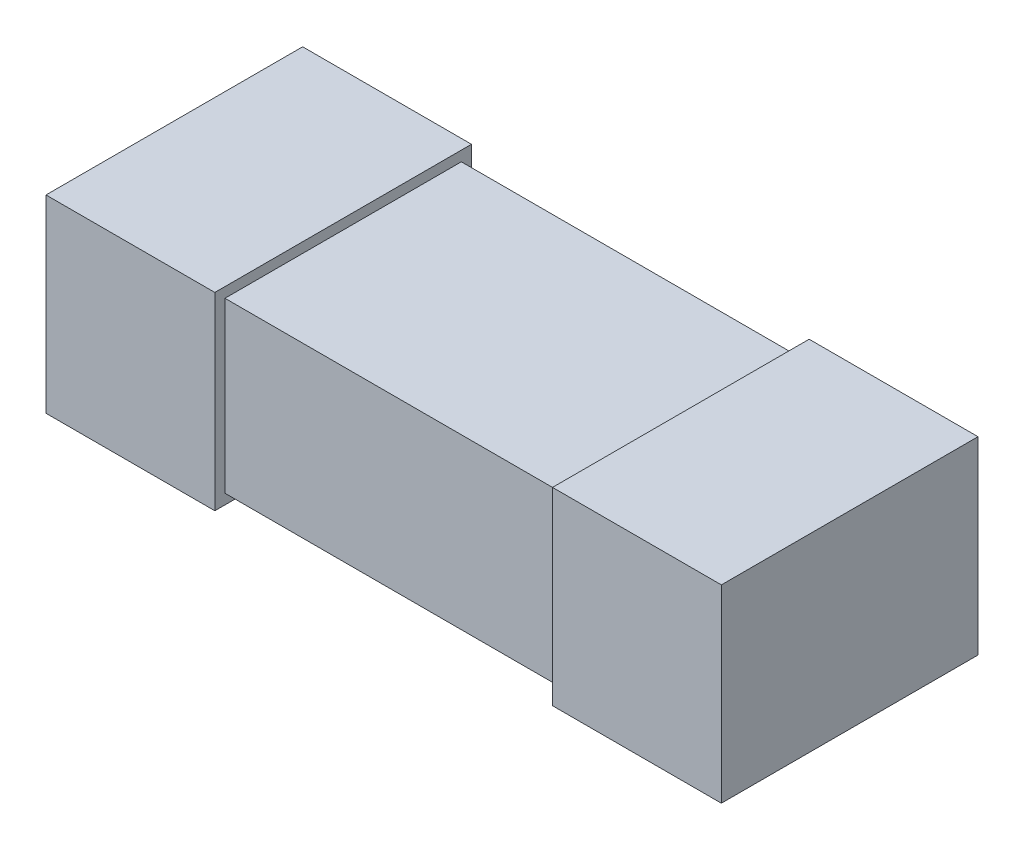
SolidWorks part; units mm, degrees
ref_plane "Front Plane" through (0, 0, 0) normal (0, 0, 1) x (1, 0, 0)
ref_plane "Top Plane" through (0, 0, 0) normal (0, 1, 0) x (1, 0, 0)
ref_plane "Right Plane" through (0, 0, 0) normal (1, 0, 0) x (0, 0, -1)
sketch "Sketch1" plane through (0, 0, 0) normal (0, 1, 0) x (1, 0, 0)
  line L0 (0, 0.35) -> (0, -0.35) construction
  line L1 (-1, -0.35) -> (1, -0.35)
  line L2 (-1, -0.35) -> (-1, 0.35)
  line L3 (-1, 0.35) -> (1, 0.35)
  line L4 (1, -0.35) -> (1, 0.35)
  dimension "D1" = 0.7
  dimension "D2" = 2
extrude "Boss-Extrude1" add sketch "Sketch1" along normal blind 0.5
sketch "Sketch2" plane through (-1, 0, 0) normal (-1, 0, 0) x (0, 0, 1)
  line L0 (-0.35, 0.5) -> (-0.35, 0) construction
  line L1 (-0.38, -0.03) -> (0.38, -0.03)
  line L2 (-0.38, -0.03) -> (-0.38, 0.53)
  line L3 (-0.38, 0.53) -> (0.38, 0.53)
  line L4 (0.38, -0.03) -> (0.38, 0.53)
  line L5 (-0.35, 0) -> (0.35, 0) construction
  line L6 (-0.35, 0.5) -> (0.35, 0.5) construction
  line L7 (0.35, 0.5) -> (0.35, 0) construction
  dimension "D1" = 0.03
  dimension "D2" = 0.03
  dimension "D3" = 0.03
  dimension "D4" = 0.03
extrude "Boss-Extrude2" add sketch "Sketch2" against normal blind 0.5
mirror "Mirror1" about plane through (0, 0, 0) normal (1, 0, 0) of "Boss-Extrude2"
